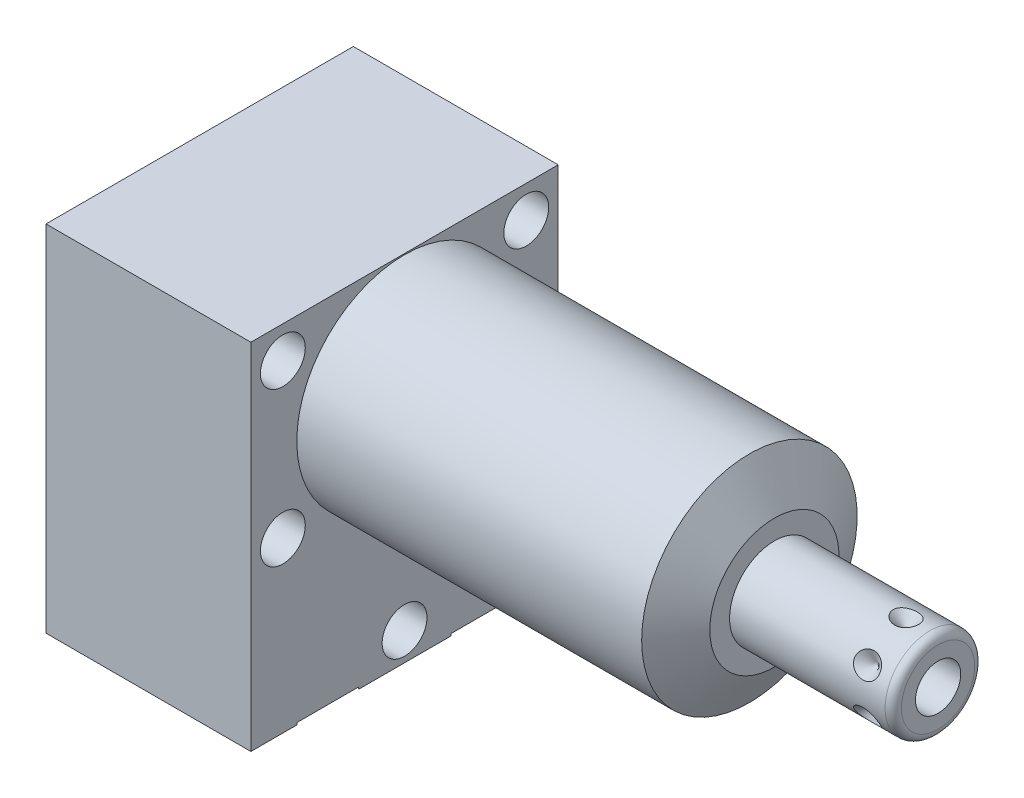
SolidWorks part; units mm, degrees
material "Alloy Steel"
ref_plane "Front Plane" through (0, 0, 0) normal (0, 0, 1) x (1, 0, 0)
ref_plane "Top Plane" through (0, 0, 0) normal (0, 1, 0) x (1, 0, 0)
ref_plane "Right Plane" through (0, 0, 0) normal (1, 0, 0) x (0, 0, -1)
ref_plane "Plane1" through (0, 0, 0) normal (1, 0, 0) x (0, 0, -1)
sketch "Sketch1" plane through (0, 0, 0) normal (1, 0, 0) x (0, 0, -1)
  line L0 (-19.05, 13.4874) -> (-19.05, -30.4546)
  line L1 (-19.05, -30.4546) -> (19.05, -30.4546)
  line L2 (19.05, -30.4546) -> (19.05, 13.4874)
  line L3 (19.05, 13.4874) -> (-19.05, 13.4874)
  line L4 (0, -32.6517) -> (0, 15.6845) construction
  dimension "D1" = 38.1
  dimension "D2" = 43.942
  dimension "D3" = 13.4874
extrude "Extrude1" add sketch "Sketch1" along normal blind 45.847 and the other way blind 25.4
ref_plane "Plane2" through (0, 0, 0) normal (1, 0, 0) x (0, 0, -1)
sketch "Sketch2" plane through (0, 0, 0) normal (1, 0, 0) x (0, 0, -1)
  line L0 (-14.6964, 0) -> (14.6964, 0) construction
  line L5 (19.05, 13.4874) -> (-19.05, 13.4874)
  line L6 (-19.05, 13.4874) -> (-19.05, -30.4546)
  line L7 (-19.05, -30.4546) -> (19.05, -30.4546)
  line L8 (19.05, -30.4546) -> (19.05, 13.4874)
  line L9 (19.05, 13.4874) -> (-19.05, 13.4874)
  line L10 (-19.05, 13.4874) -> (-19.05, -30.4546)
  line L11 (-19.05, -30.4546) -> (19.05, -30.4546)
  line L12 (19.05, -30.4546) -> (19.05, 13.4874)
  circle A0 centre (0, 0) radius 13.3604
  dimension "D1" = 26.7208
  dimension "D2" = 0
extrude "Cut-Extrude1" cut sketch "Sketch2" along normal up to next
ref_plane "Plane3" through (0, 0, 0) normal (0, 0, 1) x (1, 0, 0)
sketch "Sketch3" plane through (0, 0, 0) normal (0, 0, 1) x (1, 0, 0)
  line L0 (42.7527, 13.3604) -> (45.847, 8.001)
  line L1 (42.598, 0) -> (46.0017, 0) construction
  line L2 (45.847, 13.3604) -> (45.847, 8.001)
  line L3 (45.847, 13.3604) -> (42.7527, 13.3604)
  line L4 (45.847, 13.3604) -> (0, 13.3604) construction
  line L5 (45.847, -13.3604) -> (45.847, 13.3604) construction
  dimension "D1" = 30
  dimension "D2" = 16.002
revolve "Cut-Revolve1" cut sketch "Sketch3" angle 360 about L1
ref_plane "Plane4" through (-22.733, -19.8374, 9.525) normal (0, 0, 1) x (0, 1, 0)
sketch "S2D0002" plane through (-22.733, -19.8374, 9.525) normal (0, 0, 1) x (0, 1, 0)
  line L0 (-0.8128, 0) -> (3.7338, 0)
  line L1 (3.7338, 0) -> (3.2938, -2.0701)
  line L2 (3.2938, -2.0701) -> (2.6416, -2.7223)
  line L3 (2.6416, -2.7223) -> (2.6416, -13.97)
  line L4 (2.6416, -13.97) -> (-0.8128, -13.97)
  line L5 (-0.8128, -13.97) -> (-0.8128, 0)
  line L6 (-0.8128, -14.6685) -> (-0.8128, 0.6985) construction
  line L7 (19.8374, -65.4857) -> (19.8374, -22.733) construction
  dimension "D1" = 13.97
  dimension "D2" = 20.6502
  dimension "D3" = 3.4544
  dimension "D4" = 4.5466
revolve "Cut-Revolve2" cut sketch "S2D0002" angle 360 about L6
ref_plane "Plane5" through (-22.733, -19.8374, -9.525) normal (0, 0, 1) x (0, 1, 0)
sketch "Sketch5" plane through (-22.733, -19.8374, -9.525) normal (0, 0, 1) x (0, 1, 0)
  line L0 (-0.8128, 0) -> (3.7338, 0)
  line L1 (3.7338, 0) -> (3.2938, -2.0701)
  line L2 (3.2938, -2.0701) -> (2.6416, -2.7223)
  line L3 (2.6416, -2.7223) -> (2.6416, -13.97)
  line L4 (2.6416, -13.97) -> (-0.8128, -13.97)
  line L5 (-0.8128, -13.97) -> (-0.8128, 0)
  line L6 (-0.8128, -14.6685) -> (-0.8128, 0.6985) construction
  line L7 (19.8374, -65.4857) -> (19.8374, -22.733) construction
  dimension "D1" = 13.97
  dimension "D2" = 20.6502
revolve "Cut-Revolve3" cut sketch "Sketch5" angle 360 about L6
ref_plane "Plane6" through (-8.7376, -30.2006, 9.525) normal (0, 0, 1) x (-1, 0, 0)
sketch "Sketch14" plane through (-25.4, 0, 0) normal (-1, 0, 0) x (0, 0, 1)
  circle A0 centre (-9.525, -20.6502) radius 7.9375
  circle A1 centre (9.525, -20.6502) radius 7.9375
  dimension "D1" = 15.875
extrude "Cut-Extrude2" cut sketch "Sketch14" against normal blind 2.667
sketch "Sketch6" plane through (-8.7376, -30.2006, 9.525) normal (0, 0, 1) x (-1, 0, 0)
  line L0 (16.6624, -43.688) -> (16.6624, 0.254) construction
  line L1 (6.1836, 0) -> (5.641, -2.5527)
  line L2 (5.641, -2.5527) -> (4.9771, -3.2166)
  line L3 (4.9771, -3.2166) -> (4.9771, -17.272)
  line L4 (4.9771, -17.272) -> (0, -17.272)
  line L5 (0, -17.272) -> (0, 0)
  line L6 (0, -18.1356) -> (0, 0.8636) construction
  line L7 (6.1836, 0) -> (9.5237, 0)
  line L8 (9.5237, 0) -> (9.5237, 0.254)
  line L9 (16.6624, 0.254) -> (-8.7376, 0.254) construction
  line L10 (9.5237, 0.254) -> (0, 0.254)
  line L11 (0, 0.254) -> (0, 0)
  dimension "D1" = 19.0475
  dimension "D2" = 0.254
  dimension "D3" = 16.6624
revolve "Cut-Revolve4" cut sketch "Sketch6" angle 360 about L6
ref_plane "Plane7" through (-8.7376, -30.2006, -9.525) normal (0, 0, 1) x (-1, 0, 0)
sketch "Sketch7" plane through (-8.7376, -30.2006, -9.525) normal (0, 0, 1) x (-1, 0, 0)
  line L0 (16.6624, -43.688) -> (16.6624, 0.254) construction
  line L1 (6.1849, 0) -> (5.6423, -2.5527)
  line L2 (5.6423, -2.5527) -> (4.9784, -3.2166)
  line L3 (4.9784, -3.2166) -> (4.9784, -17.272)
  line L4 (4.9784, -17.272) -> (0, -17.272)
  line L5 (0, -17.272) -> (0, 0)
  line L6 (0, -18.1356) -> (0, 0.8636) construction
  line L7 (6.1849, 0) -> (9.5237, 0)
  line L8 (9.5237, 0) -> (-8.7376, 0) construction
  line L9 (9.5237, 0) -> (9.5237, 0.254)
  line L10 (16.6624, 0.254) -> (-8.7376, 0.254) construction
  line L11 (9.5237, 0.254) -> (0, 0.254)
  line L12 (0, 0.254) -> (0, 0)
  dimension "D1" = 16.6624
  dimension "D2" = 9.9568
  dimension "D3" = 19.0475
revolve "Cut-Revolve5" cut sketch "Sketch7" angle 360 about L6
ref_plane "Plane8" through (0, 0, 0) normal (0, 0, 1) x (1, 0, 0)
sketch "Sketch8" plane through (0, 0, 0) normal (0, 0, 1) x (1, 0, 0)
  line L0 (45.847, 0) -> (45.847, 5.5562)
  line L1 (45.847, 5.5562) -> (65.1256, 5.5562)
  line L2 (66.1416, 4.5403) -> (66.1416, 0)
  line L3 (66.1416, 0) -> (45.847, 0)
  line L4 (44.8323, 0) -> (67.1563, 0) construction
  line L5 (45.847, -8.001) -> (45.847, 8.001) construction
  line L6 (-25.4, 13.4874) -> (-25.4, -30.4546) construction
  arc A0 (66.1416, 4.5403) -> (65.1256, 5.5562) centre (65.1256, 4.5403) ccw
  point P0 (45.847, 0)
  dimension "D3" = 1.016
  dimension "D1" = 91.5416
  dimension "D2" = 11.1125
revolve "Revolve1" add sketch "Sketch8" angle 360 about L4
ref_plane "Plane9" through (66.1416, -2.8067, 0) normal (0, 0, 1) x (0, -1, 0)
sketch "S2D0001" plane through (66.1416, -2.8067, 0) normal (0, 0, 1) x (0, -1, 0)
  line L0 (0, 0) -> (0, -10.16)
  line L1 (0, -10.16) -> (-2.8067, -11.8464)
  line L2 (0, 0) -> (-2.8067, 0)
  line L3 (-2.8067, 0) -> (-2.8067, -11.8464)
  line L4 (-2.8067, -12.4388) -> (-2.8067, 0.5923) construction
  line L5 (1.7335, 0) -> (-7.3469, 0) construction
  dimension "D1" = 5.6134
  dimension "D2" = 10.16
  dimension "D3" = 59
revolve "Cut-Revolve6" cut sketch "S2D0001" angle 360 about L4
ref_plane "Plane10" through (-25.4, -30.2006, 0) normal (0, -1, 0) x (0, 0, -1)
sketch "Sketch10" plane through (-25.4, -30.2006, 0) normal (0, -1, 0) x (0, 0, -1)
  circle A0 centre (-9.525, 16.6624) radius 6.4389
  circle A1 centre (-9.525, 16.6624) radius 6.1836 construction
  dimension "D1" = 12.8778
extrude "Extrude2" add sketch "Sketch10" along normal blind 1.651
sketch "Sketch11" plane through (-22.733, 0, 0) normal (-1, 0, 0) x (0, 0, 1)
  circle A0 centre (9.525, -20.6502) radius 4.8006
  circle A1 centre (9.525, -20.6502) radius 4.5466 construction
  dimension "D1" = 9.6012
ref_plane "Plane11" through (-25.4, 0, 0) normal (1, 0, 0) x (0, 0, -1)
extrude "Extrude3" add sketch "Sketch11" along normal up to surface (2.667 mm away) up to plane "Plane11"
ref_plane "Plane12" through (62.1792, -5.5562, 0) normal (0, 0, 1) x (-1, 0, 0)
sketch "Sketch12" plane through (62.1792, -5.5562, 0) normal (0, 0, 1) x (-1, 0, 0)
  line L0 (0, 0) -> (1.5875, 0)
  line L1 (1.5875, 0) -> (0, -1.5875)
  line L2 (0, 0) -> (0, -1.5875)
  line L3 (0, -3.434) -> (0, 0.0794) construction
  line L4 (16.3322, 0) -> (-2.9464, 0) construction
  line L5 (-3.9624, -1.016) -> (-3.9624, -10.0965) construction
  dimension "D1" = 3.9624
  dimension "D2" = 45
  dimension "D3" = 3.175
revolve "Cut-Revolve7" cut sketch "Sketch12" angle 360 about L3
pattern_circular "CirPattern1" count 6 over 360 about axis through (45.848, 0, 0) along (-1, 0, 0) of "Cut-Revolve7"
hole_wizard "Hole1" positions "Sketch17" profile "Sketch16" legacy end condition up to next
sketch "Sketch17" plane through (0, 0, 0) normal (1, 0, 0) x (0, 0, -1)
  line L0 (0, 0) -> (0, 17.9298) construction
  line L1 (0, 0) -> (-24.6425, 0) construction
  point P0 (-15.0876, 9.525)
  point P10 (-15.0876, -9.525)
  point P12 (15.0876, 9.525)
  point P13 (15.0876, -9.525)
  point P14 (0, -26.9748)
  dimension "D1" = 9.525
  dimension "D2" = 15.0876
  dimension "D3" = 26.9748
sketch "Sketch16" plane through (0, 9.525, 15.0876) normal (0, 1, 0) x (0, 0, -1)
  line L0 (0, 0) -> (0, 25.4)
  line L1 (0, 25.4) -> (2.7813, 25.4)
  line L2 (2.7813, 25.4) -> (2.7813, 0)
  line L3 (2.7813, 0) -> (0, 0)
  line L4 (0, 110) -> (0, -10) construction
  dimension "Diameter" = 5.5626
  dimension "Depth" = 25.4
